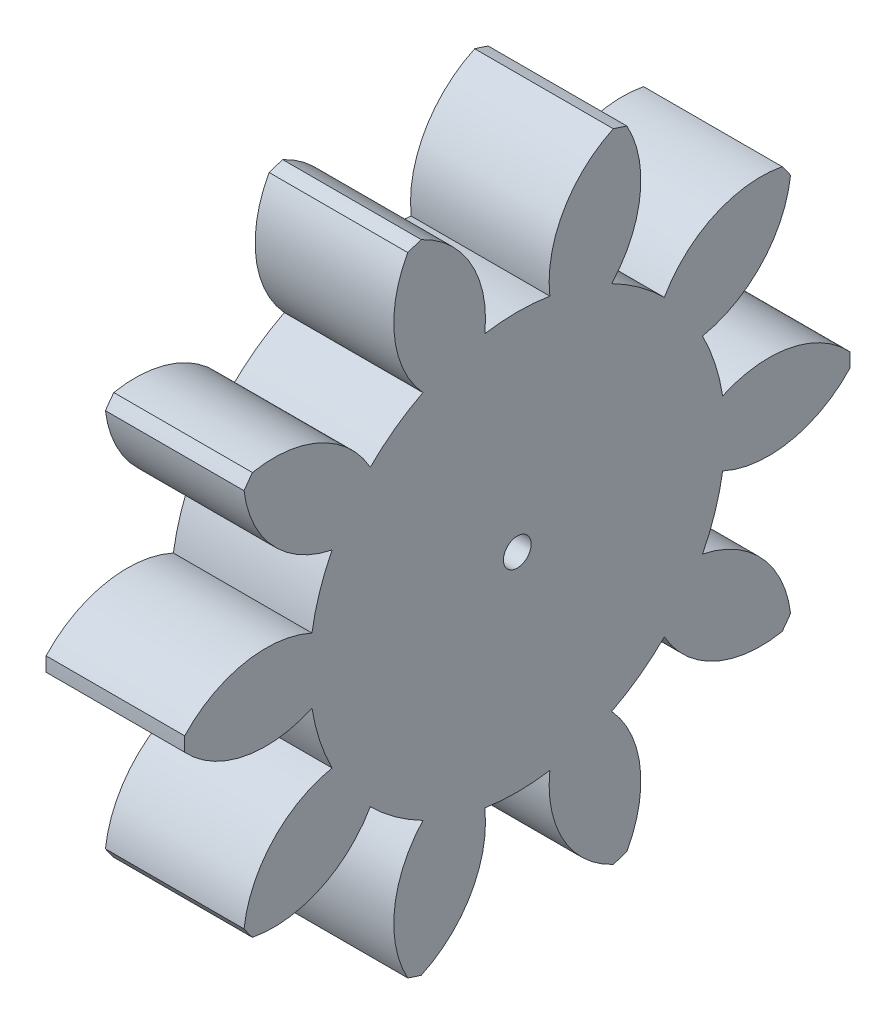
SolidWorks part; units mm, degrees
ref_plane "Plane1" through (0, 0, 0) normal (0, 0, 1) x (1, 0, 0)
ref_plane "Plane2" through (0, 0, 0) normal (0, 1, 0) x (1, 0, 0)
ref_plane "Plane3" through (0, 0, 0) normal (1, 0, 0) x (0, 0, -1)
other "Configuration Table"
sketch "HoldingSke" plane through (0, 0, 0) normal (0, 1, 0) x (1, 0, 0)
  line L0 (0, 0) -> (0.4924, -0.0868)
  line L1 (-15, 0) -> (100, 0) construction
  line L2 (0, 0) -> (-2.1039, 2.3779)
  line L3 (0, 0) -> (-11.863, 4.5341)
  line L4 (0, 0) -> (8.5048, 1.4996)
  line L5 (0, 0) -> (-46.8476, -17.4728)
  line L6 (0, 0) -> (-4.1448, -2.7965)
  line L7 (-2.1039, 2.3779) -> (8.6586, 51.2059)
  line L8 (-76.2, 54.61) -> (-76.1, 54.61)
  line L9 (-71.009, 38.7566) -> (-53.1078, 45.2721)
  line L10 (-76.2, 71.12) -> (104.1128, 71.12)
  line L11 (0, 0) -> (-5, 0)
  line L12 (-76.2, 101.6) -> (-76.133, 101.6)
  line L13 (24.9733, 27.94) -> (52.9518, 28.4284)
  line L14 (24.9733, 27.94) -> (24.9743, 27.94)
  line L15 (24.9733, 27.94) -> (100.4006, 29.5858)
  line L16 (-63.627, -2) -> (-12.827, -2)
  circle A0 centre (0, 0) radius 0.5
  circle A1 centre (0, 0) radius 7.499
  circle A2 centre (0, 0) radius 37.5
  circle A3 centre (0, 0) radius 0.5
  dimension "MHD" = 14.998
  dimension "Hub_dia" = 75
  dimension "Bore" = 1
  dimension "MBD" = 1
  dimension "Num_teeth" = 10
  dimension "Pitch" = 0.5
  dimension "Overall_len" = 50
  dimension "Show_teeth" = 10
  dimension "Thickness" = 5
  dimension "OAL" = 50.0001
  dimension "T_dim" = 0.1
  dimension "Ap" = 20
  dimension "H" = 19.05
  dimension "Pitch_radius" = 180.3128
  dimension "Width" = 5
  dimension "Backlash" = 0.067
  dimension "Addendum_fac" = 1
  dimension "Dedendum_fac" = 1.25
  dimension "Clearance_fac" = 0.25
  dimension "Dedendum_add" = 0.001
  dimension "Module" = 2
sketch "BasProSke" plane through (0, 0, 0) normal (0, 1, 0) x (1, 0, 0)
  line L0 (-10, 0) -> (60, 0) construction
  line L1 (0, 0) -> (0, 12)
  line L2 (0, 0) -> (5, 0)
  line L3 (5, 0) -> (5, 12)
  line L4 (5, 12) -> (0, 12)
  dimension "Thickness" = 5
  dimension "Diameter" = 24
revolve "Base-Revolve" add sketch "BasProSke" angle 360 about L0
sketch "TooCutSke" plane through (0, 0, 0) normal (1, 0, 0) x (0, 0, -1)
  line L1 (0, 0) -> (0, 107) construction
  line L2 (0, 0) -> (-1.6814, 9.8576) construction
  line L3 (0, 0) -> (-6.1153, 18.8209) construction
  line L4 (-1.6814, 9.8576) -> (-3.0576, 9.4105) construction
  arc A0 (1.1737, 7.4066) -> (-1.1737, 7.4066) centre (0, 0) ccw
  arc A1 (3.4979, 11.5054) -> (-3.4979, 11.5054) centre (0, 0) ccw
  circle A2 centre (0, 0) radius 10 construction
  circle A3 centre (0, 0) radius 9.3969 construction
  arc A4 (-1.1737, 7.4066) -> (-3.4979, 11.5054) centre (-5.1477, 7.8615) ccw
  arc A5 (3.4979, 11.5054) -> (1.1737, 7.4066) centre (5.1477, 7.8615) ccw
  dimension "Root_dia" = 14.998
  dimension "Overcut_dia" = 24.0508
  dimension "Pitch_dia" = 20
  dimension "Base_dia" = 18.7939
  dimension "Flank_rad" = 4
  dimension "Half_ang" = 18
  dimension "Half_CT" = 1.4471
extrude "ToothCut" cut sketch "TooCutSke" along normal through all
fillet "Breaks" [suppressed] radius 0.04
fillet "RootFillets" [suppressed] radius 0.501
pattern_circular "TeethCuts" count 10 every 36 about axis through (-10, 0, 0) along (1, 0, 0) of "ToothCut", "RootFillets", "Breaks"
sketch "HubNeaOneSke" plane through (0, 0, 0) normal (-1, 0, 0) x (0, 0, 1)
  circle A0 centre (0, 0) radius 7.499
  dimension "Diameter" = 14.998
extrude "HubNearOne" [suppressed] add sketch "HubNeaOneSke" along normal blind 45.0001
sketch "HubNeaBotSke" plane through (0, 0, 0) normal (-1, 0, 0) x (0, 0, 1)
  circle A0 centre (0, 0) radius 7.499
  dimension "Diameter" = 14.998
extrude "HubNearBoth" [suppressed] add sketch "HubNeaBotSke" along normal blind 22.5
ref_plane "FarPln" through (5, 0, 0) normal (1, 0, 0) x (0, 0, -1)
sketch "HubFarSke" plane through (5, 0, 0) normal (1, 0, 0) x (0, 0, -1)
  circle A0 centre (0, 0) radius 7.499
  dimension "Diameter" = 14.998
extrude "HubFar" [suppressed] add sketch "HubFarSke" along normal blind 22.5
sketch "BorSke" plane through (0, 0, 0) normal (1, 0, 0) x (0, 0, -1)
  circle A0 centre (0, 0) radius 0.5
  dimension "Diameter" = 1
extrude "Bore" cut sketch "BorSke" along normal mid plane 100.0001
sketch "KeySke" plane through (0, 0, 0) normal (1, 0, 0) x (0, 0, -1)
  line L0 (-0.05, 0) -> (-0.05, 0.6)
  line L1 (-0.05, 0.6) -> (0.05, 0.6)
  line L2 (0.05, 0.6) -> (0.05, 0)
  line L3 (0, 0) -> (0, 34) construction
  line L4 (-0.05, 0) -> (0.05, 0)
  dimension "Offset" = 0.6
  dimension "Width" = 0.1
extrude "Keyway" [suppressed] cut sketch "KeySke" along normal mid plane 100.0001
pattern_circular "Keyway2" [suppressed] count 2 every 90 about axis through (-10, 0, 0) along (1, 0, 0)
equation "' \"Module@HoldingSke\" = 6.35"
equation "' \"Num_teeth@HoldingSke\" = 12"
equation "' \"Ap@HoldingSke\" =  20"
equation "' \"Ap@HoldingSke\" = 20"
equation "' \"Width@HoldingSke\" = 0.5 * 25.4"
equation "' \"Hub_dia@HoldingSke\"= 1 * 25.4"
equation "' \"Hub_dia@HoldingSke\" = 1 * 25.4"
equation "' \"Overall_len@HoldingSke\" = 1.0 * 25.4"
equation "' \"Bore@HoldingSke\" = 0.75 * 25.4"
equation "' \"T_dim@HoldingSke\" = 0.1 * 25.4"
equation "' \"Width@KeySke\" = 0.25 * 25.4"
equation "' \"Show_teeth@HoldingSke\" = 13"
equation "' \"Backlash@HoldingSke\" = 0.009 * 25.4"
equation "' \"Addendum_fac@HoldingSke\" = 1.0"
equation "' \"Dedendum_fac@HoldingSke\" = 1.25"
equation "' \"Dedendum_add@HoldingSke\" = 0.00005 * 25.4"
equation "' \"Clearance_fac@HoldingSke\" = 0.25"
equation "\"Pitch@HoldingSke\" = 1 / \"Module@HoldingSke\""
equation "\"Overcut_dia@TooCutSke\" = (\"Num_teeth@HoldingSke\" + 2 * \"Addendum_fac@HoldingSke\") / \"Pitch@HoldingSke\" + 0.002 * 25.4"
equation "\"Pitch_dia@TooCutSke\" = \"Num_teeth@HoldingSke\" / \"Pitch@HoldingSke\""
equation "\"Base_dia@TooCutSke\" = \"Num_teeth@HoldingSke\" / \"Pitch@HoldingSke\" * cos((\"Ap@HoldingSke\"  * 3.14159265 / 180))"
equation "\"Root_dia@TooCutSke\" = (\"Num_teeth@HoldingSke\" + 2) / \"Pitch@HoldingSke\" - 2 * (\"Addendum_fac@HoldingSke\" + \"Dedendum_fac@HoldingSke\") / \"Pitch@HoldingSke\" - \"Dedendum_add@HoldingSke\" * 2"
equation "\"Half_ang@TooCutSke\" = 180 / \"Num_teeth@HoldingSke\""
equation "\"Half_CT@TooCutSke\" = \"Num_teeth@HoldingSke\" / \"Pitch@HoldingSke\" * sin((3.14159265 / 2 / \"Num_teeth@HoldingSke\")) / 2 - 7 * \"Backlash@HoldingSke\" / 4"
equation "\"Flank_rad@TooCutSke\" = \"Num_teeth@HoldingSke\" / \"Pitch@HoldingSke\" / 5"
equation "\"Radius@RootFillets\" = \"Clearance_fac@HoldingSke\" / \"Pitch@HoldingSke\" + \"Dedendum_add@HoldingSke\""
equation "\"Break_rad@Breaks\" = 0.02 / \"Pitch@HoldingSke\""
equation "\"Thickness@HoldingSke\" = \"Width@HoldingSke\""
equation "\"OAL@HoldingSke\" = \"Thickness@HoldingSke\""
equation "\"MHD@HoldingSke\" = (\"Num_teeth@HoldingSke\" + 2) / \"Pitch@HoldingSke\" - 2 * (\"Addendum_fac@HoldingSke\" + \"Dedendum_fac@HoldingSke\")  / \"Pitch@HoldingSke\" - \"Dedendum_add@HoldingSke\" * 2"
equation "\"MBD@HoldingSke\" = (\"Num_teeth@HoldingSke\" + 2) / \"Pitch@HoldingSke\" - 2 * (\"Addendum_fac@HoldingSke\" + \"Dedendum_fac@HoldingSke\")  / \"Pitch@HoldingSke\" - \"Dedendum_add@HoldingSke\" * 2 - 0.002 * 25.4"
equation "\"MHD@HoldingSke\" = ((sgn( \"MHD@HoldingSke\" - \"Hub_dia@HoldingSke\" )-1)*( \"MHD@HoldingSke\" - \"Hub_dia@HoldingSke\" ))/-2+ \"Hub_dia@HoldingSke\""
equation "\"MBD@HoldingSke\" = ((sgn( \"MBD@HoldingSke\" - \"Bore@HoldingSke\" )-1)*( \"MBD@HoldingSke\" - \"Bore@HoldingSke\" ))/-2+ \"Bore@HoldingSke\""
equation "\"OAL@HoldingSke\" = ((sgn( \"OAL@HoldingSke\" - \"Overall_len@HoldingSke\" )+1)*( \"OAL@HoldingSke\" - \"Overall_len@HoldingSke\" ))/2 + \"Overall_len@HoldingSke\" + 0.000002 * 25.4"
equation "\"Num_teeth@TeethCuts\" = int( \"Show_teeth@HoldingSke\" ) + 1"
equation "\"Num_teeth@TeethCuts\" = ((sgn( \"Num_teeth@TeethCuts\" - \"Num_teeth@HoldingSke\" )-1)*( \"Num_teeth@TeethCuts\" - \"Num_teeth@HoldingSke\" ))/-2+ \"Num_teeth@HoldingSke\""
equation "\"Num_teeth@TeethCuts\" = ((sgn( \"Num_teeth@TeethCuts\" - 2.0)+1)*( \"Num_teeth@TeethCuts\" - 2.0))/2 +2.0"
equation "\"Angle@TeethCuts\" = 360.0 / \"Num_teeth@HoldingSke\""
equation "\"Diameter@BasProSke\" = (\"Num_teeth@HoldingSke\" + 2 * \"Addendum_fac@HoldingSke\") / \"Pitch@HoldingSke\""
equation "\"Thickness@BasProSke\"  = \"Thickness@HoldingSke\""
equation "' \"Fillet_rad@BasProSke\" =  \"Thickness@HoldingSke\" * 0.05"
equation "' \"Fillet_rad@BasProSke\" = \"Thickness@HoldingSke\" * 0.05"
equation "\"MHD@HoldingSke\" = ((sgn( \"MHD@HoldingSke\" - \"Root_dia@TooCutSke\" )-1)*( \"MHD@HoldingSke\" - \"Root_dia@TooCutSke\" ))/-2+ \"Root_dia@TooCutSke\""
equation "\"Diameter@HubNeaOneSke\" = \"MHD@HoldingSke\""
equation "\"Length@HubNearOne\" = \"OAL@HoldingSke\" - \"Thickness@BasProSke\""
equation "\"Diameter@HubNeaBotSke\" = \"MHD@HoldingSke\""
equation "\"Length@HubNearBoth\" = ( \"OAL@HoldingSke\" - \"Thickness@BasProSke\" ) / 2.0"
equation "\"Thickness@FarPln\" = \"Thickness@BasProSke\""
equation "\"Diameter@HubFarSke\" = \"MHD@HoldingSke\""
equation "\"Length@HubFar\" = ( \"OAL@HoldingSke\" - \"Thickness@BasProSke\" ) / 2.0"
equation "\"Diameter@BorSke\" = \"MBD@HoldingSke\""
equation "\"D1@Bore\" = \"OAL@HoldingSke\" * 2.0"
equation "\"D1@Keyway\" = \"OAL@HoldingSke\" * 2.0"
equation "\"Offset@KeySke\" = \"T_dim@HoldingSke\" + \"MBD@HoldingSke\" / 2.0"
